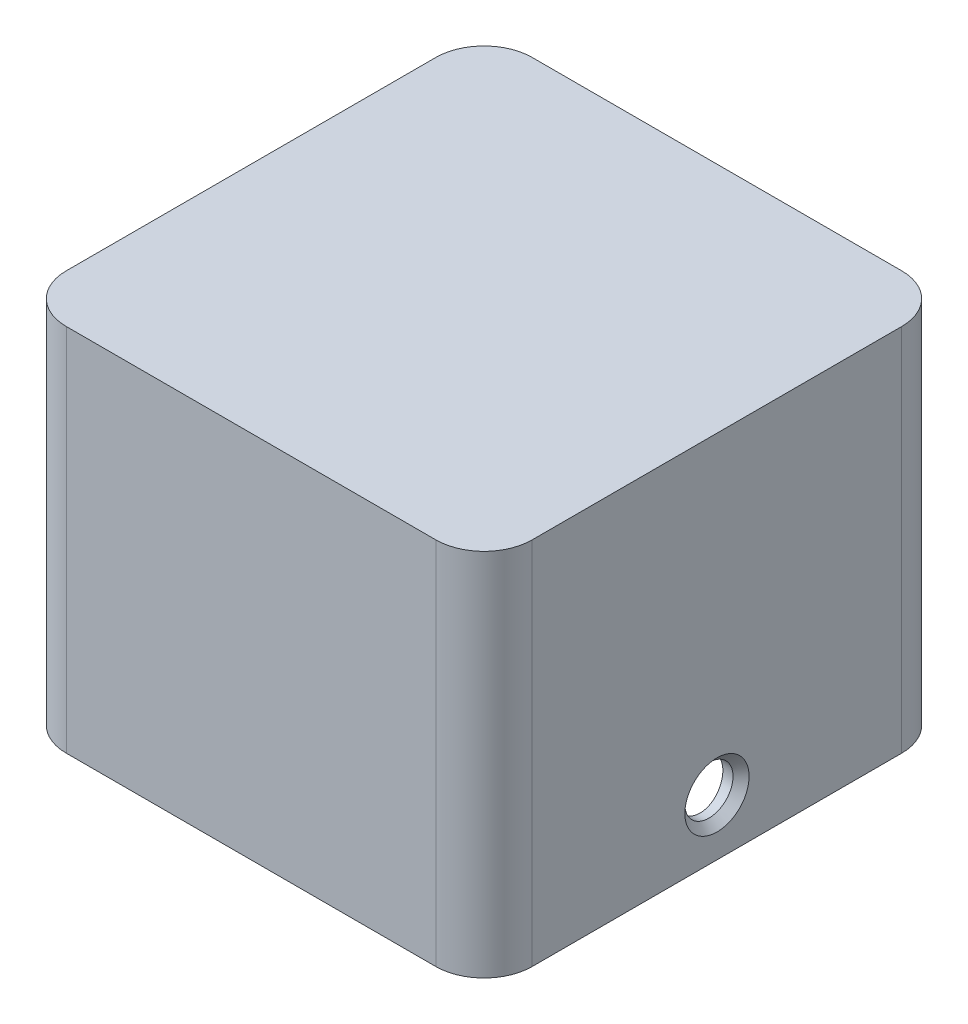
SolidWorks part; units mm, degrees
ref_plane "Front Plane" through (0, 0, 0) normal (0, 0, 1) x (1, 0, 0)
ref_plane "Top Plane" through (0, 0, 0) normal (0, 1, 0) x (1, 0, 0)
ref_plane "Right Plane" through (0, 0, 0) normal (1, 0, 0) x (0, 0, -1)
sketch "Sketch1" plane through (0, 0, 0) normal (0, 1, 0) x (1, 0, 0)
  line L1 (0, 0) -> (29, 0)
  line L2 (0, 0) -> (0, 29)
  line L3 (0, 29) -> (29, 29)
  line L4 (29, 0) -> (29, 29)
  dimension "D1" = 29
  dimension "D2" = 29
extrude "Boss-Extrude1" add sketch "Sketch1" along normal blind 23
fillet "Fillet1" radius 3 4 edges at (0, 11.5, -29) (29, 11.5, -29) (29, 11.5, 0) (0, 11.5, 0)
sketch "Sketch2" plane through (0, 0, 0) normal (0, -1, 0) x (1, 0, 0)
  line L0 (0, -14.5) -> (29, -14.5) construction
  line L1 (0, -26) -> (0, -3) construction
  line L2 (29, -3) -> (29, -26) construction
  circle A0 centre (14.5, -14.5) radius 13.45
  dimension "D1" = 26.9
extrude "Cut-Extrude1" cut sketch "Sketch2" against normal blind 6.75 contours A0
ref_plane "Plane1" through (0, 6.75, 0) normal (0, -1, 0) x (-1, 0, 0)
ref_plane "Plane2" through (14.5, 0, 0) normal (1, 0, 0) x (0, 0, -1)
sketch "Sketch6" plane through (14.5, 0, 0) normal (1, 0, 0) x (0, 0, -1)
  line L0 (14.5, 23) -> (14.5, 6.75) construction
  line L1 (3, 23) -> (26, 23) construction
  line L2 (-14.795, 6.75) -> (14.795, 6.75) construction
  line L3 (14.5, 6.75) -> (14.5, 19.6)
  line L4 (14.5, 6.75) -> (27.35, 6.75)
  arc A0 (14.5, 19.6) -> (27.35, 6.75) centre (14.5, 6.75) cw
  dimension "D1" = 12.85
  dimension "D2" = 12.85
revolve "Cut-Revolve1" cut sketch "Sketch6" angle 360 about L3
sketch "Sketch7" plane through (0, 0, 0) normal (0, -1, 0) x (1, 0, 0)
  line L0 (14.5, 0) -> (14.5, -29) construction
  line L1 (3, 0) -> (26, 0) construction
  line L2 (26, -29) -> (3, -29) construction
  line L3 (29, -14.5) -> (0, -14.5) construction
  line L6 (29, -3) -> (29, -26) construction
  line L7 (0, -26) -> (0, -3) construction
  circle A0 centre (3, -3) radius 0.85
  circle A1 centre (26, -3) radius 0.85
  circle A2 centre (26, -26) radius 0.85
  circle A3 centre (3, -26) radius 0.85
  dimension "D1" = 1.7
  dimension "D5" = 1.7
  dimension "D6" = 1.7
  dimension "D2" = 11.5
  dimension "D3" = 11.5
  dimension "D4" = 11.5
extrude "Cut-Extrude2" cut sketch "Sketch7" against normal blind 10
sketch "Sketch8" plane through (0, 0, 0) normal (-1, 0, 0) x (0, 0, 1)
  line L0 (-14.5, 0) -> (-14.5, 23) construction
  line L1 (-26, 0) -> (-3, 0) construction
  line L2 (-26, 23) -> (-3, 23) construction
  circle A0 centre (-14.5, 3.5) radius 1.5
  dimension "D1" = 3
  dimension "D2" = 3.5
extrude "Cut-Extrude3" cut sketch "Sketch8" against normal through all
chamfer "Chamfer1" distance 0.5 angle 45 2 edges at (29, 3.5, -13) (0, 3.5, -13)
equation "\"D2@Sketch1\"=\"D1@Sketch1\""
equation "\"D2@Sketch6\"=\"D1@Sketch6\""
equation "\"D3@Sketch7\"=\"D2@Sketch7\""
equation "\"D5@Sketch7\"=\"D6@Sketch7\""
equation "\"D1@Sketch7\"=\"D6@Sketch7\""
